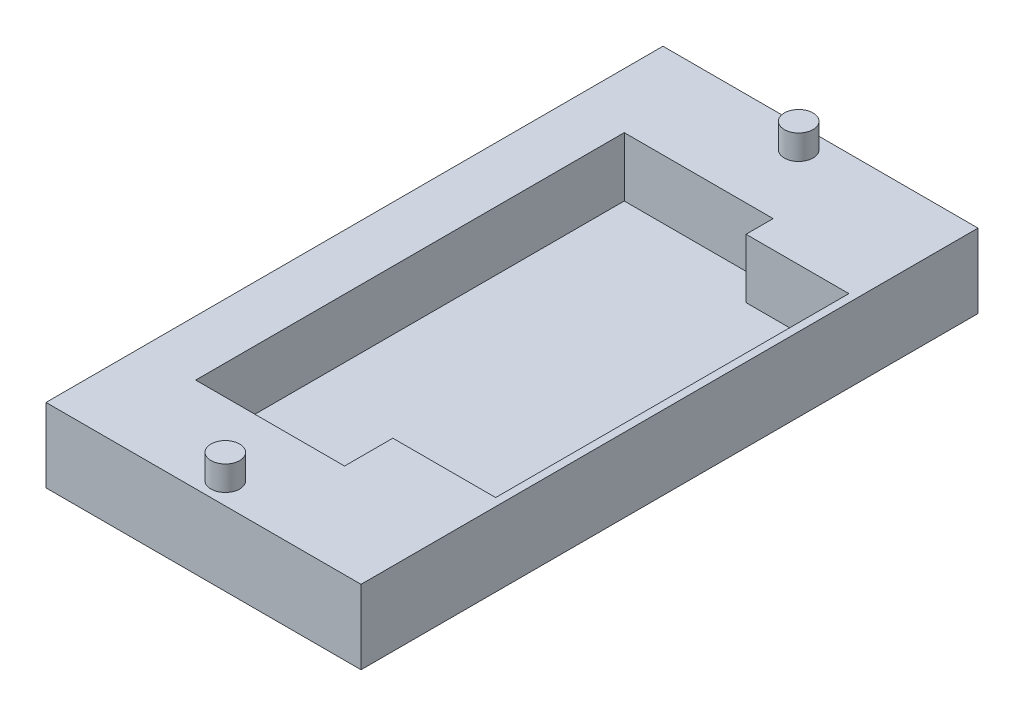
SolidWorks part; units mm, degrees
ref_plane "Alzado" through (0, 0, 0) normal (0, 0, 1) x (1, 0, 0)
ref_plane "Planta" through (0, 0, 0) normal (0, 1, 0) x (1, 0, 0)
ref_plane "Vista lateral" through (0, 0, 0) normal (1, 0, 0) x (0, 0, -1)
sketch "Croquis1" plane through (0, 0, 0) normal (0, 1, 0) x (1, 0, 0)
  line L1 (22.5, 37.5) -> (-22.5, 37.5)
  line L2 (22.5, 37.5) -> (22.5, -37.5)
  line L3 (22.5, -37.5) -> (-22.5, -37.5)
  line L4 (-22.5, 37.5) -> (-22.5, -37.5)
  line L5 (22.5, 37.5) -> (-22.5, -37.5) construction
  line L6 (22.5, -37.5) -> (-22.5, 37.5) construction
  point P0 (0, 0)
  dimension "D1" = 45
  dimension "D2" = 75
extrude "Saliente-Extruir1" add sketch "Croquis1" along normal blind 9
sketch "Croquis2" plane through (0, 9, 0) normal (0, 1, 0) x (1, 0, 0)
  line L1 (9.05, 26.05) -> (-9.05, 26.05)
  line L2 (9.05, 26.05) -> (9.05, -26.05)
  line L3 (9.05, -26.05) -> (-9.05, -26.05)
  line L4 (-9.05, 26.05) -> (-9.05, -26.05)
  line L5 (9.05, 26.05) -> (-9.05, -26.05) construction
  line L6 (9.05, -26.05) -> (-9.05, 26.05) construction
  line L7 (9.05, 22.7544) -> (21.55, 22.7544)
  line L8 (9.05, 22.7544) -> (9.05, -20.1845)
  line L9 (9.05, -20.1845) -> (21.55, -20.1845)
  line L10 (21.55, 22.7544) -> (21.55, -20.1845)
  point P0 (0, 0)
  dimension "D1" = 18.1
  dimension "D2" = 52.1
  dimension "D3" = 12.5
extrude "Cortar-Extruir9" cut sketch "Croquis2" against normal blind 7.2
sketch "Croquis3" plane through (0, 9, 0) normal (0, 1, 0) x (1, 0, 0)
  line L0 (-22.5, -37.5) -> (22.5, -37.5) construction
  line L1 (-22.5, 37.5) -> (-15.7956, 37.5)
  line L2 (-22.5, 37.5) -> (-22.5, -37.5)
  line L3 (-22.5, -37.5) -> (-15.7956, -37.5)
  line L4 (-15.7956, 37.5) -> (-15.7956, -37.5)
  dimension "D1" = 6.7044
extrude "Cortar-Extruir10" cut sketch "Croquis3" against normal blind 9
sketch "Croquis4" plane through (0, 9, 0) normal (0, 1, 0) x (1, 0, 0)
  line L0 (-15.7956, -37.5) -> (22.5, -37.5) construction
  line L1 (22.5, 37.5) -> (-15.7956, 37.5) construction
  circle A0 centre (3.3522, -34.85) radius 1.745
  circle A1 centre (3.3522, 34.85) radius 1.75
  dimension "D1" = 3.49
  dimension "D4" = 3.5
  dimension "D2" = 2.65
  dimension "D3" = 2.65
extrude "Saliente-Extruir2" add sketch "Croquis4" along normal blind 3
